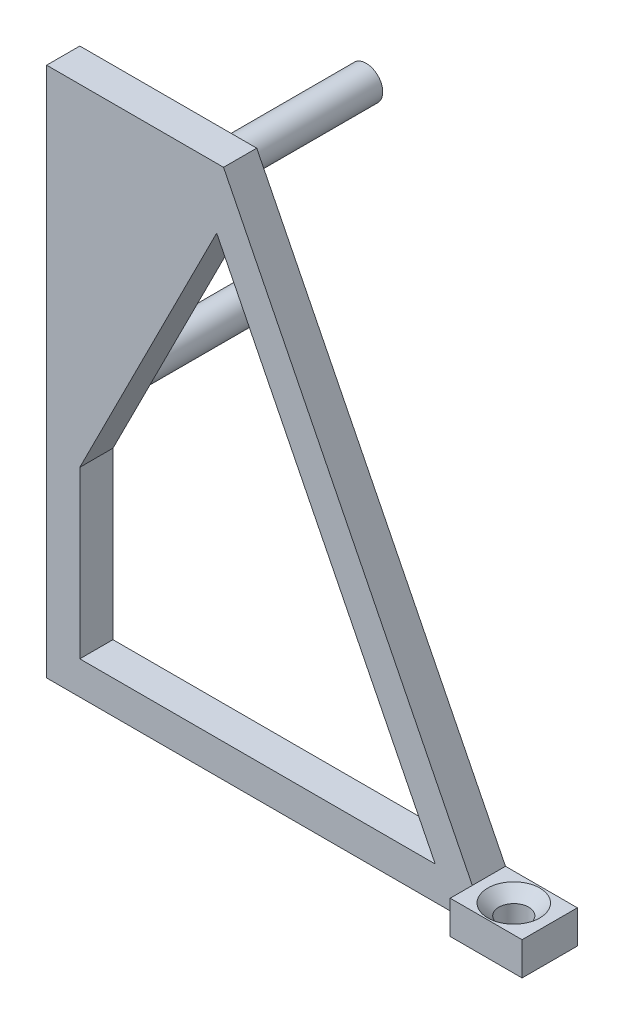
SolidWorks part; units mm, degrees
ref_plane "Přední rovina" through (0, 0, 0) normal (0, 0, 1) x (1, 0, 0)
ref_plane "Horní rovina" through (0, 0, 0) normal (0, 1, 0) x (1, 0, 0)
ref_plane "Pravá rovina" through (0, 0, 0) normal (1, 0, 0) x (0, 0, -1)
sketch "Skica1" plane through (0, 0, 0) normal (0, 0, 1) x (1, 0, 0)
  line L0 (0, 0) -> (0, 48)
  line L1 (0, 48) -> (16, 48)
  line L2 (0, 0) -> (40, 0)
  line L3 (16, 48) -> (38.5, 3)
  line L4 (3, 3) -> (35.1459, 3)
  line L5 (3, 3) -> (3, 18)
  line L6 (3, 18) -> (15.3783, 42.5353)
  line L7 (15.3783, 42.5353) -> (35.1459, 3)
  line L8 (40, 0) -> (45, 0)
  line L9 (45, 0) -> (45, 3)
  line L10 (45, 3) -> (38.5, 3)
  circle A0 centre (12.9, 45.1) radius 1.5
  circle A1 centre (2.5, 22.9) radius 1.5
  dimension "D10" = 3
  dimension "D14" = 3
  dimension "D1" = 48
  dimension "D2" = 16
  dimension "D3" = 40
  dimension "D4" = 3
  dimension "D5" = 15
  dimension "D6" = 3
  dimension "D7" = 5.5
  dimension "D8" = 3
  dimension "D9" = 2.9
  dimension "D11" = 12.9
  dimension "D12" = 2.5
  dimension "D13" = 25.1
  dimension "D15" = 5
extrude "Přidat vysunutím1" add sketch "Skica1" along normal blind 3
sketch "Skica2" plane through (0, 0, 0) normal (0, 0, -1) x (-1, 0, 0)
  line L0 (-16, 48) -> (0, 48) construction
  line L1 (0, 48) -> (0, 0) construction
  circle A0 centre (-12.9, 45.1) radius 1.5
  circle A1 centre (-2.5, 22.9) radius 1.5
  dimension "D2" = 3
  dimension "D3" = 3
  dimension "D1" = 2.9
  dimension "D4" = 12.9
extrude "Přidat vysunutím2" add sketch "Skica2" along normal blind 13 and the other way blind 3
sketch "Skica3" plane through (0, 0, 3) normal (0, 0, 1) x (1, 0, 0)
  line L0 (0, 0) -> (45, 0) construction
  line L1 (45, 3) -> (38.5, 3)
  line L2 (45, 3) -> (45, 0)
  line L3 (45, 0) -> (38.5, 0)
  line L4 (38.5, 3) -> (38.5, 0)
  dimension "D1" = 6.5
extrude "Přidat vysunutím3" add sketch "Skica3" along normal blind 2
sketch "Skica4" plane through (0, 3, 0) normal (0, 1, 0) x (1, 0, 0)
  line L0 (45, 0) -> (38.5, 0) construction
  line L1 (45, -5) -> (45, 0) construction
  circle A0 centre (41.75, -2.5) radius 1.35
  dimension "D1" = 2.7
  dimension "D2" = 2.5
  dimension "D3" = 3.25
extrude "Odebrat vysunutím1" cut sketch "Skica4" against normal blind 3
chamfer "Zkosení1" distance 1 angle 45 1 edges at (40.4, 3, 2.5)
